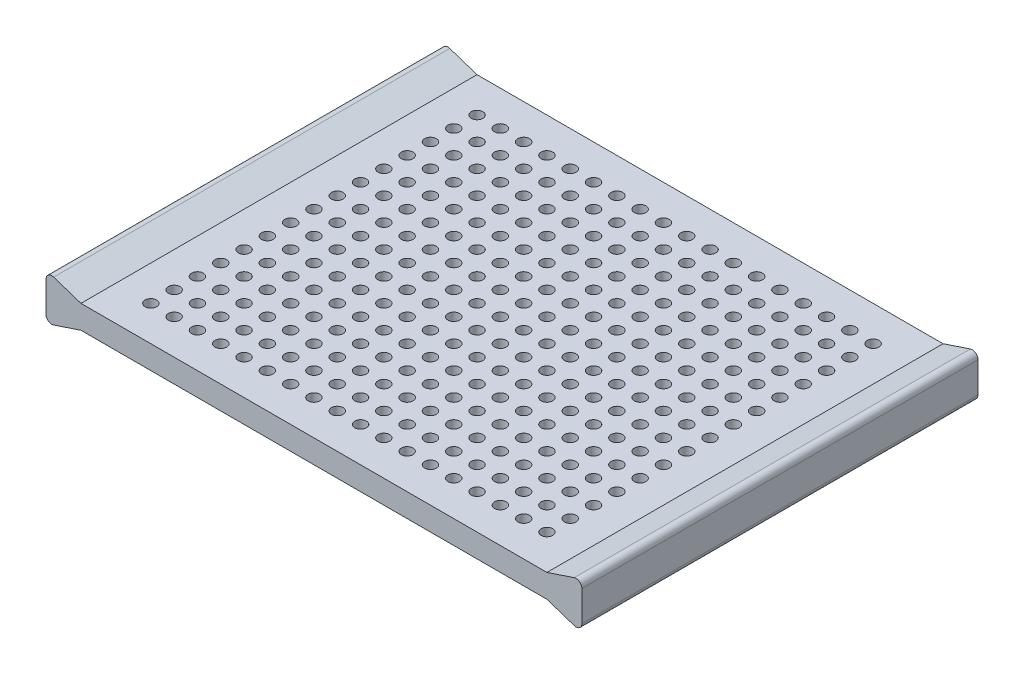
SolidWorks part; units mm, degrees
ref_plane "Front Plane" through (0, 0, 0) normal (0, 0, 1) x (1, 0, 0)
ref_plane "Top Plane" through (0, 0, 0) normal (0, 1, 0) x (1, 0, 0)
ref_plane "Right Plane" through (0, 0, 0) normal (1, 0, 0) x (0, 0, -1)
sketch "Sketch1" plane through (0, 0, 0) normal (0, 0, 1) x (1, 0, 0)
  line L1 (0, 0) -> (200, 0)
  line L2 (0, 0) -> (0, 10)
  line L3 (0, 10) -> (200, 10)
  line L4 (200, 0) -> (200, 10)
  dimension "D1" = 10
  dimension "D2" = 200
extrude "Mesh Block" add sketch "Sketch1" along normal blind 170
sketch "Sketch2" plane through (0, 10, 0) normal (0, 1, 0) x (1, 0, 0)
  line L0 (0, -155) -> (15, -155) construction
  line L1 (0, -170) -> (0, 0) construction
  line L2 (200, -170) -> (0, -170) construction
  line L3 (15, -170) -> (15, 0) construction
  line L4 (200, 0) -> (0, 0) construction
  line L5 (185, -170) -> (185, 0) construction
  line L6 (200, -170) -> (200, 0) construction
  line L7 (15, -155) -> (25, -155) construction
  line L8 (15, -155) -> (15, -145) construction
  line L9 (15, -65) -> (15, -55) construction
  circle A0 centre (15, -155) radius 2.5
  circle A1 centre (25, -155) radius 2.5
  circle A2 centre (35, -155) radius 2.5
  circle A3 centre (45, -155) radius 2.5
  circle A4 centre (55, -155) radius 2.5
  circle A5 centre (65, -155) radius 2.5
  circle A6 centre (75, -155) radius 2.5
  circle A7 centre (85, -155) radius 2.5
  circle A8 centre (95, -155) radius 2.5
  circle A9 centre (105, -155) radius 2.5
  circle A10 centre (115, -155) radius 2.5
  circle A11 centre (125, -155) radius 2.5
  circle A12 centre (135, -155) radius 2.5
  circle A13 centre (145, -155) radius 2.5
  circle A14 centre (155, -155) radius 2.5
  circle A15 centre (165, -155) radius 2.5
  circle A16 centre (175, -155) radius 2.5
  circle A17 centre (185, -155) radius 2.5
  circle A18 centre (15, -145) radius 2.5
  circle A19 centre (185, -145) radius 2.5
  circle A20 centre (175, -145) radius 2.5
  circle A21 centre (165, -145) radius 2.5
  circle A22 centre (155, -145) radius 2.5
  circle A23 centre (145, -145) radius 2.5
  circle A24 centre (135, -145) radius 2.5
  circle A25 centre (125, -145) radius 2.5
  circle A26 centre (115, -145) radius 2.5
  circle A27 centre (105, -145) radius 2.5
  circle A28 centre (25, -145) radius 2.5
  circle A29 centre (35, -145) radius 2.5
  circle A30 centre (45, -145) radius 2.5
  circle A31 centre (55, -145) radius 2.5
  circle A32 centre (65, -145) radius 2.5
  circle A33 centre (75, -145) radius 2.5
  circle A34 centre (85, -145) radius 2.5
  circle A35 centre (95, -145) radius 2.5
  circle A36 centre (15, -135) radius 2.5
  circle A37 centre (185, -135) radius 2.5
  circle A38 centre (175, -135) radius 2.5
  circle A39 centre (165, -135) radius 2.5
  circle A40 centre (155, -135) radius 2.5
  circle A41 centre (145, -135) radius 2.5
  circle A42 centre (135, -135) radius 2.5
  circle A43 centre (125, -135) radius 2.5
  circle A44 centre (115, -135) radius 2.5
  circle A45 centre (105, -135) radius 2.5
  circle A46 centre (25, -135) radius 2.5
  circle A47 centre (35, -135) radius 2.5
  circle A48 centre (45, -135) radius 2.5
  circle A49 centre (55, -135) radius 2.5
  circle A50 centre (65, -135) radius 2.5
  circle A51 centre (75, -135) radius 2.5
  circle A52 centre (85, -135) radius 2.5
  circle A53 centre (95, -135) radius 2.5
  circle A54 centre (15, -125) radius 2.5
  circle A55 centre (185, -125) radius 2.5
  circle A56 centre (175, -125) radius 2.5
  circle A57 centre (165, -125) radius 2.5
  circle A58 centre (155, -125) radius 2.5
  circle A59 centre (145, -125) radius 2.5
  circle A60 centre (135, -125) radius 2.5
  circle A61 centre (125, -125) radius 2.5
  circle A62 centre (115, -125) radius 2.5
  circle A63 centre (105, -125) radius 2.5
  circle A64 centre (25, -125) radius 2.5
  circle A65 centre (35, -125) radius 2.5
  circle A66 centre (45, -125) radius 2.5
  circle A67 centre (55, -125) radius 2.5
  circle A68 centre (65, -125) radius 2.5
  circle A69 centre (75, -125) radius 2.5
  circle A70 centre (85, -125) radius 2.5
  circle A71 centre (95, -125) radius 2.5
  circle A72 centre (15, -115) radius 2.5
  circle A73 centre (185, -115) radius 2.5
  circle A74 centre (175, -115) radius 2.5
  circle A75 centre (165, -115) radius 2.5
  circle A76 centre (155, -115) radius 2.5
  circle A77 centre (145, -115) radius 2.5
  circle A78 centre (135, -115) radius 2.5
  circle A79 centre (125, -115) radius 2.5
  circle A80 centre (115, -115) radius 2.5
  circle A81 centre (105, -115) radius 2.5
  circle A82 centre (25, -115) radius 2.5
  circle A83 centre (35, -115) radius 2.5
  circle A84 centre (45, -115) radius 2.5
  circle A85 centre (55, -115) radius 2.5
  circle A86 centre (65, -115) radius 2.5
  circle A87 centre (75, -115) radius 2.5
  circle A88 centre (85, -115) radius 2.5
  circle A89 centre (95, -115) radius 2.5
  circle A90 centre (15, -105) radius 2.5
  circle A91 centre (185, -105) radius 2.5
  circle A92 centre (175, -105) radius 2.5
  circle A93 centre (165, -105) radius 2.5
  circle A94 centre (155, -105) radius 2.5
  circle A95 centre (145, -105) radius 2.5
  circle A96 centre (135, -105) radius 2.5
  circle A97 centre (125, -105) radius 2.5
  circle A98 centre (115, -105) radius 2.5
  circle A99 centre (105, -105) radius 2.5
  circle A100 centre (25, -105) radius 2.5
  circle A101 centre (35, -105) radius 2.5
  circle A102 centre (45, -105) radius 2.5
  circle A103 centre (55, -105) radius 2.5
  circle A104 centre (65, -105) radius 2.5
  circle A105 centre (75, -105) radius 2.5
  circle A106 centre (85, -105) radius 2.5
  circle A107 centre (95, -105) radius 2.5
  circle A108 centre (15, -95) radius 2.5
  circle A109 centre (185, -95) radius 2.5
  circle A110 centre (175, -95) radius 2.5
  circle A111 centre (165, -95) radius 2.5
  circle A112 centre (155, -95) radius 2.5
  circle A113 centre (145, -95) radius 2.5
  circle A114 centre (135, -95) radius 2.5
  circle A115 centre (125, -95) radius 2.5
  circle A116 centre (115, -95) radius 2.5
  circle A117 centre (105, -95) radius 2.5
  circle A118 centre (25, -95) radius 2.5
  circle A119 centre (35, -95) radius 2.5
  circle A120 centre (45, -95) radius 2.5
  circle A121 centre (55, -95) radius 2.5
  circle A122 centre (65, -95) radius 2.5
  circle A123 centre (75, -95) radius 2.5
  circle A124 centre (85, -95) radius 2.5
  circle A125 centre (95, -95) radius 2.5
  circle A126 centre (15, -85) radius 2.5
  circle A127 centre (185, -85) radius 2.5
  circle A128 centre (175, -85) radius 2.5
  circle A129 centre (165, -85) radius 2.5
  circle A130 centre (155, -85) radius 2.5
  circle A131 centre (145, -85) radius 2.5
  circle A132 centre (135, -85) radius 2.5
  circle A133 centre (125, -85) radius 2.5
  circle A134 centre (115, -85) radius 2.5
  circle A135 centre (105, -85) radius 2.5
  circle A136 centre (25, -85) radius 2.5
  circle A137 centre (35, -85) radius 2.5
  circle A138 centre (45, -85) radius 2.5
  circle A139 centre (55, -85) radius 2.5
  circle A140 centre (65, -85) radius 2.5
  circle A141 centre (75, -85) radius 2.5
  circle A142 centre (85, -85) radius 2.5
  circle A143 centre (95, -85) radius 2.5
  circle A144 centre (15, -75) radius 2.5
  circle A145 centre (185, -75) radius 2.5
  circle A146 centre (175, -75) radius 2.5
  circle A147 centre (165, -75) radius 2.5
  circle A148 centre (155, -75) radius 2.5
  circle A149 centre (145, -75) radius 2.5
  circle A150 centre (135, -75) radius 2.5
  circle A151 centre (125, -75) radius 2.5
  circle A152 centre (115, -75) radius 2.5
  circle A153 centre (105, -75) radius 2.5
  circle A154 centre (25, -75) radius 2.5
  circle A155 centre (35, -75) radius 2.5
  circle A156 centre (45, -75) radius 2.5
  circle A157 centre (55, -75) radius 2.5
  circle A158 centre (65, -75) radius 2.5
  circle A159 centre (75, -75) radius 2.5
  circle A160 centre (85, -75) radius 2.5
  circle A161 centre (95, -75) radius 2.5
  circle A162 centre (15, -65) radius 2.5
  circle A163 centre (185, -65) radius 2.5
  circle A164 centre (175, -65) radius 2.5
  circle A165 centre (165, -65) radius 2.5
  circle A166 centre (155, -65) radius 2.5
  circle A167 centre (145, -65) radius 2.5
  circle A168 centre (135, -65) radius 2.5
  circle A169 centre (125, -65) radius 2.5
  circle A170 centre (115, -65) radius 2.5
  circle A171 centre (105, -65) radius 2.5
  circle A172 centre (25, -65) radius 2.5
  circle A173 centre (35, -65) radius 2.5
  circle A174 centre (45, -65) radius 2.5
  circle A175 centre (55, -65) radius 2.5
  circle A176 centre (65, -65) radius 2.5
  circle A177 centre (75, -65) radius 2.5
  circle A178 centre (85, -65) radius 2.5
  circle A179 centre (95, -65) radius 2.5
  circle A180 centre (15, -55) radius 2.5
  circle A181 centre (25, -55) radius 2.5
  circle A182 centre (35, -55) radius 2.5
  circle A183 centre (45, -55) radius 2.5
  circle A184 centre (55, -55) radius 2.5
  circle A185 centre (65, -55) radius 2.5
  circle A186 centre (75, -55) radius 2.5
  circle A187 centre (85, -55) radius 2.5
  circle A188 centre (95, -55) radius 2.5
  circle A189 centre (105, -55) radius 2.5
  circle A190 centre (115, -55) radius 2.5
  circle A191 centre (125, -55) radius 2.5
  circle A192 centre (135, -55) radius 2.5
  circle A193 centre (145, -55) radius 2.5
  circle A194 centre (155, -55) radius 2.5
  circle A195 centre (165, -55) radius 2.5
  circle A196 centre (175, -55) radius 2.5
  circle A197 centre (185, -55) radius 2.5
  circle A198 centre (15, -45) radius 2.5
  circle A199 centre (25, -45) radius 2.5
  circle A200 centre (35, -45) radius 2.5
  circle A201 centre (45, -45) radius 2.5
  circle A202 centre (55, -45) radius 2.5
  circle A203 centre (65, -45) radius 2.5
  circle A204 centre (75, -45) radius 2.5
  circle A205 centre (85, -45) radius 2.5
  circle A206 centre (95, -45) radius 2.5
  circle A207 centre (105, -45) radius 2.5
  circle A208 centre (115, -45) radius 2.5
  circle A209 centre (125, -45) radius 2.5
  circle A210 centre (135, -45) radius 2.5
  circle A211 centre (145, -45) radius 2.5
  circle A212 centre (155, -45) radius 2.5
  circle A213 centre (165, -45) radius 2.5
  circle A214 centre (175, -45) radius 2.5
  circle A215 centre (185, -45) radius 2.5
  circle A216 centre (15, -35) radius 2.5
  circle A217 centre (25, -35) radius 2.5
  circle A218 centre (35, -35) radius 2.5
  circle A219 centre (45, -35) radius 2.5
  circle A220 centre (55, -35) radius 2.5
  circle A221 centre (65, -35) radius 2.5
  circle A222 centre (75, -35) radius 2.5
  circle A223 centre (85, -35) radius 2.5
  circle A224 centre (95, -35) radius 2.5
  circle A225 centre (105, -35) radius 2.5
  circle A226 centre (115, -35) radius 2.5
  circle A227 centre (125, -35) radius 2.5
  circle A228 centre (135, -35) radius 2.5
  circle A229 centre (145, -35) radius 2.5
  circle A230 centre (155, -35) radius 2.5
  circle A231 centre (165, -35) radius 2.5
  circle A232 centre (175, -35) radius 2.5
  circle A233 centre (185, -35) radius 2.5
  circle A234 centre (15, -25) radius 2.5
  circle A235 centre (25, -25) radius 2.5
  circle A236 centre (35, -25) radius 2.5
  circle A237 centre (45, -25) radius 2.5
  circle A238 centre (55, -25) radius 2.5
  circle A239 centre (65, -25) radius 2.5
  circle A240 centre (75, -25) radius 2.5
  circle A241 centre (85, -25) radius 2.5
  circle A242 centre (95, -25) radius 2.5
  circle A243 centre (105, -25) radius 2.5
  circle A244 centre (115, -25) radius 2.5
  circle A245 centre (125, -25) radius 2.5
  circle A246 centre (135, -25) radius 2.5
  circle A247 centre (145, -25) radius 2.5
  circle A248 centre (155, -25) radius 2.5
  circle A249 centre (165, -25) radius 2.5
  circle A250 centre (175, -25) radius 2.5
  circle A251 centre (185, -25) radius 2.5
  circle A252 centre (15, -15) radius 2.5
  circle A253 centre (25, -15) radius 2.5
  circle A254 centre (35, -15) radius 2.5
  circle A255 centre (45, -15) radius 2.5
  circle A256 centre (55, -15) radius 2.5
  circle A257 centre (65, -15) radius 2.5
  circle A258 centre (75, -15) radius 2.5
  circle A259 centre (85, -15) radius 2.5
  circle A260 centre (95, -15) radius 2.5
  circle A261 centre (105, -15) radius 2.5
  circle A262 centre (115, -15) radius 2.5
  circle A263 centre (125, -15) radius 2.5
  circle A264 centre (135, -15) radius 2.5
  circle A265 centre (145, -15) radius 2.5
  circle A266 centre (155, -15) radius 2.5
  circle A267 centre (165, -15) radius 2.5
  circle A268 centre (175, -15) radius 2.5
  circle A269 centre (185, -15) radius 2.5
  dimension "D4" = 5
  dimension "D1" = 15
  dimension "D2" = 15
  dimension "D3" = 15
  dimension "D6" = 10
  dimension "D8" = 10
  dimension "D10" = 10
  dimension "D5" = 18
  dimension "D7" = 10
  dimension "D9" = 6
extrude "Mesh Holes" cut sketch "Sketch2" against normal through all
sketch "Sketch3" plane through (0, 0, 170) normal (0, 0, 1) x (1, 0, 0)
  line L0 (0, 0) -> (-11.7094, -3.9031)
  line L1 (-15, -1.5314) -> (-15, 11.5314)
  line L2 (-11.7094, 13.9031) -> (0, 10)
  line L3 (-15, 5) -> (0, 5) construction
  line L4 (0, 10) -> (0, 0) construction
  line L5 (100, 0) -> (100, 10) construction
  line L6 (0, 0) -> (200, 0) construction
  line L7 (200, 10) -> (0, 10) construction
  line L8 (211.7094, 13.9031) -> (200, 10)
  line L9 (215, -1.5314) -> (215, 11.5314)
  line L10 (200, 0) -> (211.7094, -3.9031)
  line L11 (200, 0) -> (200, 10)
  line L12 (0, 0) -> (0, 10)
  arc A0 (-15, -1.5314) -> (-11.7094, -3.9031) centre (-12.5, -1.5314) ccw
  arc A1 (-11.7094, 13.9031) -> (-15, 11.5314) centre (-12.5, 11.5314) ccw
  arc A2 (211.7094, 13.9031) -> (215, 11.5314) centre (212.5, 11.5314) cw
  arc A3 (215, -1.5314) -> (211.7094, -3.9031) centre (212.5, -1.5314) cw
  point P13 (-15, -5)
  point P16 (-15, 15)
  dimension "D3" = 2.5
  dimension "D4" = 2.5
  dimension "D1" = 15
  dimension "D2" = 20
extrude "Locking Mechanism" add sketch "Sketch3" against normal up to vertex (170 mm away) up to point (0, 10, 0)
